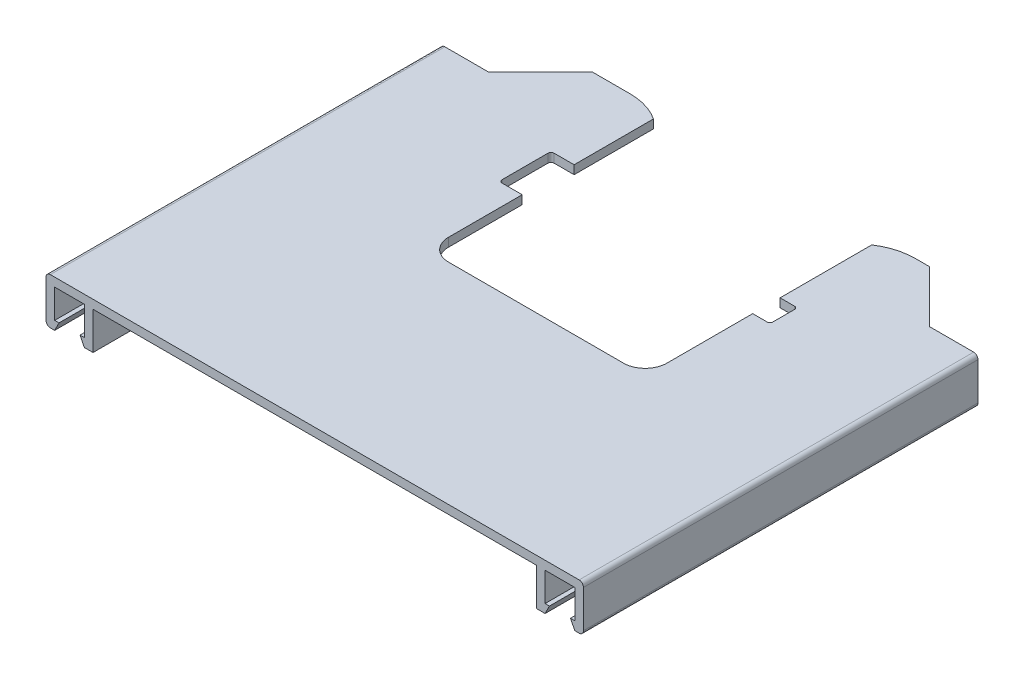
SolidWorks part; units mm, degrees
ref_plane "Front Plane" through (0, 0, 0) normal (0, 0, 1) x (1, 0, 0)
ref_plane "Top Plane" through (0, 0, 0) normal (0, 1, 0) x (1, 0, 0)
ref_plane "Right Plane" through (0, 0, 0) normal (1, 0, 0) x (0, 0, -1)
sketch "Sketch1" plane through (0, 0, 0) normal (0, 1, 0) x (1, 0, 0)
  line L1 (0, 0) -> (186.3, 0)
  line L2 (0, 0) -> (0, 72.76)
  line L3 (0, 72.76) -> (186.3, 72.76)
  line L4 (186.3, 0) -> (186.3, 72.76)
  dimension "D1" = 186.3
  dimension "D2" = 72.76
extrude "Boss-Extrude1" add sketch "Sketch1" along normal blind 3
sketch "Sketch3" plane through (0, 3, 0) normal (0, 1, 0) x (1, 0, 0)
  line L1 (0, 72.76) -> (59.3, 72.76)
  line L2 (0, 72.76) -> (0, 136.76)
  line L3 (0, 136.76) -> (59.3, 136.76)
  line L4 (59.3, 72.76) -> (59.3, 136.76)
  line L5 (186.3, 72.76) -> (134.95, 72.76)
  line L6 (186.3, 72.76) -> (186.3, 136.76)
  line L7 (186.3, 136.76) -> (134.95, 136.76)
  line L8 (134.95, 72.76) -> (134.95, 136.76)
  dimension "D1" = 59.3
  dimension "D2" = 64
  dimension "D3" = 51.35
extrude "Boss-Extrude3" add sketch "Sketch3" against normal up to vertex (3 mm away)
sketch "Sketch5" plane through (0, 3, 0) normal (0, 1, 0) x (1, 0, 0)
  line L0 (169.56, 136.76) -> (151.56, 154.76)
  line L1 (186.3, 136.76) -> (134.95, 136.76) construction
  line L2 (151.56, 154.76) -> (146.56, 154.76)
  line L3 (134.95, 151.26) -> (134.95, 136.76)
  line L4 (186.3, 0) -> (186.3, 136.76) construction
  line L5 (134.95, 136.76) -> (169.56, 136.76)
  line L6 (97.125, 72.76) -> (97.125, 169.1741) construction
  line L7 (134.95, 72.76) -> (59.3, 72.76) construction
  line L8 (59.3, 136.76) -> (16.69, 136.76)
  line L9 (59.3, 151.26) -> (59.3, 136.76)
  line L10 (34.69, 154.76) -> (47.69, 154.76)
  line L11 (16.69, 136.76) -> (34.69, 154.76)
  line L12 (59.3, 136.76) -> (0, 136.76) construction
  arc A0 (134.95, 151.26) -> (146.56, 154.76) centre (146.56, 133.754) cw
  arc A1 (59.3, 151.26) -> (47.69, 154.76) centre (47.69, 133.754) ccw
  dimension "D5" = 5
  dimension "D1" = 45
  dimension "D2" = 18
  dimension "D3" = 16.74
  dimension "D4" = 14.5
  dimension "D6" = 45
  dimension "D7" = 13
extrude "Boss-Extrude4" add sketch "Sketch5" against normal up to vertex (3 mm away)
sketch "Sketch6" plane through (0, 3, 0) normal (0, 1, 0) x (1, 0, 0)
  line L0 (59.3, 72.76) -> (59.3, 151.26) construction
  line L1 (59.3, 123.76) -> (52.3, 123.76)
  line L2 (59.3, 123.76) -> (59.3, 105.76)
  line L3 (59.3, 105.76) -> (52.3, 105.76)
  line L4 (51.3, 122.76) -> (51.3, 106.76)
  line L5 (134.95, 114.76) -> (59.3, 114.76) construction
  line L6 (134.95, 151.26) -> (134.95, 72.76) construction
  line L8 (134.95, 72.76) -> (59.3, 72.76) construction
  line L9 (139.95, 110.01) -> (134.95, 110.01)
  line L10 (140.95, 111.01) -> (140.95, 118.51)
  line L11 (134.95, 110.01) -> (134.95, 119.51)
  line L12 (139.95, 119.51) -> (134.95, 119.51)
  line L13 (140.95, 110.01) -> (134.95, 119.51) construction
  line L14 (134.95, 110.01) -> (140.95, 119.51) construction
  arc A0 (52.3, 105.76) -> (51.3, 106.76) centre (52.3, 106.76) cw
  arc A1 (52.3, 123.76) -> (51.3, 122.76) centre (52.3, 122.76) ccw
  arc A2 (140.95, 111.01) -> (139.95, 110.01) centre (139.95, 111.01) cw
  arc A3 (140.95, 118.51) -> (139.95, 119.51) centre (139.95, 118.51) ccw
  point P10 (137.95, 114.76)
  point P15 (51.3, 105.76)
  point P18 (51.3, 123.76)
  dimension "D4" = 1
  dimension "D7" = 1
  dimension "D1" = 18
  dimension "D2" = 42
  dimension "D3" = 8
  dimension "D5" = 6
  dimension "D6" = 9.5
extrude "Cut-Extrude1" cut sketch "Sketch6" against normal blind 10
sketch "Sketch9" plane through (0, 0, 0) normal (0, -1, 0) x (1, 0, 0)
  line L0 (16.69, -136.76) -> (0, -136.76) construction
  line L1 (0, 0) -> (3, 0)
  line L2 (0, 0) -> (0, -136.76)
  line L3 (0, -136.76) -> (3, -136.76)
  line L4 (3, 0) -> (3, -136.76)
  line L5 (0, 0) -> (186.3, 0) construction
  line L6 (186.3, -136.76) -> (183.3, -136.76)
  line L7 (186.3, -136.76) -> (186.3, 0)
  line L8 (186.3, 0) -> (183.3, 0)
  line L9 (183.3, -136.76) -> (183.3, 0)
  line L10 (186.3, -136.76) -> (169.56, -136.76) construction
  line L11 (13.3, 0) -> (16.3, 0)
  line L12 (13.3, 0) -> (13.3, -136.76)
  line L13 (13.3, -136.76) -> (16.3, -136.76)
  line L14 (16.3, 0) -> (16.3, -136.76)
  line L15 (173, -136.76) -> (170, -136.76)
  line L16 (173, -136.76) -> (173, 0)
  line L17 (173, 0) -> (170, 0)
  line L18 (170, -136.76) -> (170, 0)
  dimension "D1" = 3
  dimension "D2" = 10.3
  dimension "D3" = 10.3
extrude "Boss-Extrude7" add sketch "Sketch9" along normal blind 13
fillet "Fillet1" radius 7.5 2 edges at (59.3, 1.5, -72.76) (134.95, 1.5, -72.76)
sketch "Sketch10" plane through (0, 0, -136.76) normal (0, 0, -1) x (-1, 0, 0)
  line L0 (-183.3, -13) -> (-181.8, -10)
  line L1 (-181.8, -10) -> (-183.3, -10)
  line L2 (-183.3, -13) -> (-183.3, 0) construction
  line L3 (-183.3, -10) -> (-183.3, -13)
  line L4 (-178.15, 0) -> (-178.15, -13) construction
  line L5 (-183.3, 0) -> (-173, 0) construction
  line L6 (-174.5, -10) -> (-173, -10)
  line L7 (-173, -13) -> (-174.5, -10)
  line L8 (-173, -10) -> (-173, -13)
  line L9 (-13.3, 0) -> (-3, 0) construction
  line L11 (-8.15, 0) -> (-8.15, -13.0787) construction
  line L12 (-13.3, -10) -> (-13.3, -13)
  line L13 (-13.3, -13) -> (-11.8, -10)
  line L14 (-11.8, -10) -> (-13.3, -10)
  line L19 (-13.3, -13) -> (-13.3, 0) construction
  line L20 (-4.5, -10) -> (-3, -10)
  line L21 (-3, -13) -> (-4.5, -10)
  line L22 (-3, -10) -> (-3, -13)
  dimension "D1" = 3
  dimension "D2" = 1.5
extrude "Boss-Extrude8" add sketch "Sketch10" against normal up to vertex (136.76 mm away)
fillet "Fillet2" radius 1.5 4 edges at (0, -13, -68.38) (0, 3, -68.38) (186.3, -13, -68.38) (186.3, 3, -68.38)
